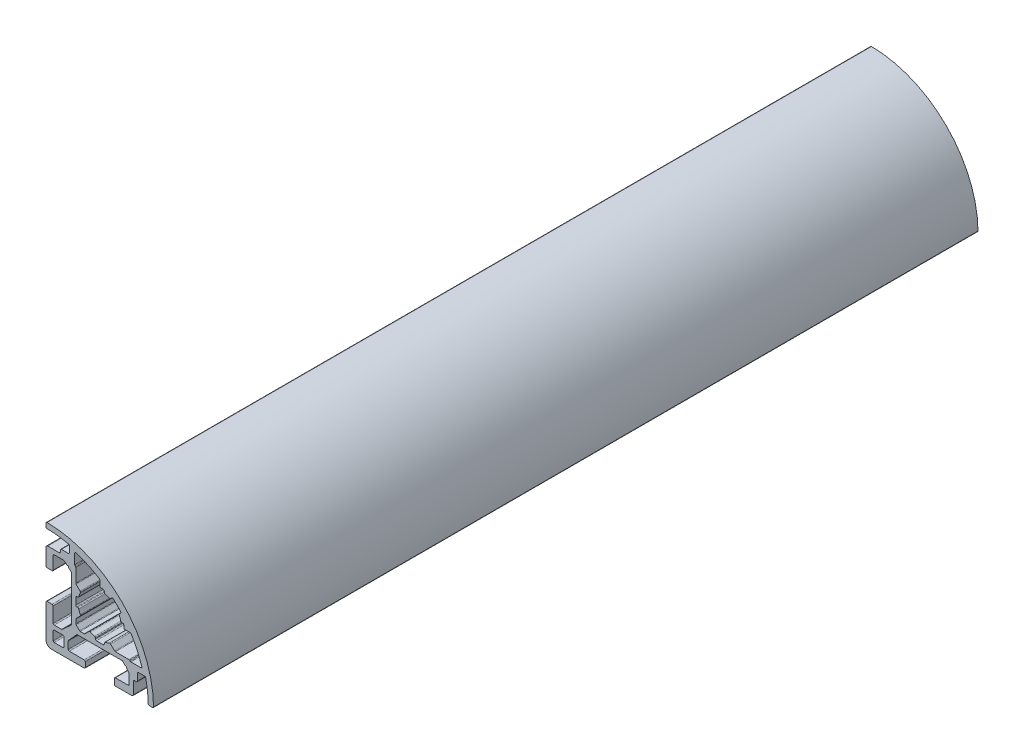
SolidWorks part; units mm, degrees
ref_plane "Plano frontal" through (0, 0, 0) normal (0, 0, 1) x (1, 0, 0)
ref_plane "Plano superior" through (0, 0, 0) normal (0, 1, 0) x (1, 0, 0)
ref_plane "Plano direito" through (0, 0, 0) normal (1, 0, 0) x (0, 0, -1)
ref_plane "Plano1" through (0, 0, 0) normal (0, 0, -1) x (-1, 0, 0)
sketch "Esboço1" plane through (0, 0, 0) normal (0, 0, -1) x (-1, 0, 0)
  line L0 (12.7, -13) -> (10.3, -13)
  line L1 (10, -12.7) -> (10, -10.3)
  line L2 (10.3, -10) -> (12.7, -10)
  line L3 (13, -10.3) -> (13, -12.7)
  line L4 (-0.95, 6.7) -> (-0.3, 6.7)
  line L5 (0, 7) -> (0, 8.4776)
  line L6 (7, 11.4273) -> (7, 8.6799)
  line L7 (6.9121, 8.4678) -> (6.7879, 8.3435)
  line L8 (6.7, 8.1314) -> (6.7, 4.3494)
  line L9 (6.6121, 4.1372) -> (5.4871, 3.0123)
  line L10 (6.1579, 1.25) -> (6.4, 1.25)
  line L11 (6.7, 0.95) -> (6.7, -0.95)
  line L12 (6.4, -1.25) -> (6.1579, -1.25)
  line L13 (5.4871, -3.0123) -> (6.6121, -4.1372)
  line L14 (6.7, -4.3494) -> (6.7, -5.4396)
  line L15 (6.6121, -5.6517) -> (5.6517, -6.6121)
  line L16 (5.4395, -6.7) -> (4.3494, -6.7)
  line L17 (4.1373, -6.6121) -> (3.0123, -5.4871)
  line L18 (1.25, -6.1579) -> (1.25, -6.4)
  line L19 (0.95, -6.7) -> (-0.95, -6.7)
  line L20 (-1.25, -6.4) -> (-1.25, -6.1579)
  line L21 (-3.0123, -5.4871) -> (-4.1373, -6.6121)
  line L22 (-4.3494, -6.7) -> (-8.1314, -6.7)
  line L23 (-8.3435, -6.7879) -> (-8.4678, -6.9121)
  line L24 (-8.6799, -7) -> (-11.4273, -7)
  line L25 (-8.4777, 0) -> (-7, 0)
  line L26 (-6.7, 0.3) -> (-6.7, 0.95)
  line L27 (-6.4, 1.25) -> (-6.1579, 1.25)
  line L28 (-5.4871, 3.0123) -> (-5.7974, 3.3226)
  line L29 (-3.3226, 5.7974) -> (-3.0123, 5.4871)
  line L30 (-1.25, 6.1579) -> (-1.25, 6.4)
  line L31 (7.9882, 6.432) -> (8.7045, 7.072)
  line L32 (8.7045, 7.072) -> (8.7283, 7.4958)
  line L33 (8.7283, 7.4958) -> (9.1516, 7.472)
  line L34 (9.1516, 7.472) -> (9.8678, 8.112)
  line L35 (10.08, 8.1999) -> (12.7001, 8.1998)
  line L36 (13.0001, 7.8998) -> (13, 4.3499)
  line L37 (13.3, 4.0499) -> (14.7, 4.0498)
  line L38 (15, 4.3498) -> (15, 8.8999)
  line L39 (14.5, 9.3999) -> (11.3, 9.3999)
  line L40 (11, 9.6999) -> (11, 10.1999)
  line L41 (10.7, 10.4999) -> (8.8, 10.4999)
  line L42 (8.5, 10.7999) -> (8.5, 12.51)
  line L43 (15, 13.7984) -> (15, 14.6985)
  line L44 (-14.6985, -15) -> (-13.7984, -15)
  line L45 (-12.5105, -8.5) -> (-10.8005, -8.5)
  line L46 (-10.5005, -8.8) -> (-10.5005, -10.7)
  line L47 (-10.2005, -11) -> (-9.7004, -11)
  line L48 (-9.4004, -11.3) -> (-9.4004, -14.5)
  line L49 (-8.9004, -15) -> (-4.3505, -15)
  line L50 (-4.0505, -14.7) -> (-4.0504, -13.3)
  line L51 (-4.3504, -13) -> (-7.9005, -12.9999)
  line L52 (-8.2005, -12.6999) -> (-8.2004, -10.0799)
  line L53 (-8.1126, -9.8677) -> (-7.4725, -9.1515)
  line L54 (-7.4725, -9.1515) -> (-7.4963, -8.728)
  line L55 (-7.4963, -8.728) -> (-7.0727, -8.7042)
  line L56 (-7.0727, -8.7042) -> (-6.4326, -7.988)
  line L57 (-6.2205, -7.9001) -> (6.2197, -7.9001)
  line L58 (6.4318, -7.988) -> (8.7117, -10.4679)
  line L59 (8.7996, -10.6801) -> (8.7996, -12.7001)
  line L60 (8.4996, -13.0001) -> (4.3496, -13.0001)
  line L61 (4.0496, -13.3001) -> (4.0496, -14.7)
  line L62 (4.3496, -15) -> (13.5, -15)
  line L63 (15, -13.5) -> (15, -4.3503)
  line L64 (14.7, -4.0503) -> (13.2999, -4.0503)
  line L65 (12.9999, -4.3503) -> (12.9999, -8.5003)
  line L66 (12.6999, -8.8003) -> (10.6798, -8.8003)
  line L67 (10.4677, -8.7124) -> (7.9878, -6.4325)
  line L68 (7.9003, -6.2203) -> (7.9003, 6.2198)
  arc A0 (10.3, -13) -> (10, -12.7) centre (10.3, -12.7) cw
  arc A1 (10, -10.3) -> (10.3, -10) centre (10.3, -10.3) cw
  arc A2 (12.7, -10) -> (13, -10.3) centre (12.7, -10.3) cw
  arc A3 (13, -12.7) -> (12.7, -13) centre (12.7, -12.7) cw
  arc A4 (-0.3, 6.7) -> (0, 7) centre (-0.3, 7) ccw
  arc A5 (0, 8.4776) -> (0.1408, 8.7319) centre (0.3, 8.4776) cw
  arc A6 (0.1408, 8.7319) -> (6.6101, 11.7135) centre (15, -15) cw
  arc A7 (6.6101, 11.7135) -> (7, 11.4273) centre (6.7, 11.4273) cw
  arc A8 (7, 8.6799) -> (6.9121, 8.4678) centre (6.7, 8.6799) cw
  arc A9 (6.7879, 8.3435) -> (6.7, 8.1314) centre (7, 8.1314) ccw
  arc A10 (6.7, 4.3494) -> (6.6121, 4.1372) centre (6.4, 4.3494) cw
  arc A11 (5.4871, 3.0123) -> (5.43, 2.6678) centre (5.6993, 2.8001) ccw
  arc A12 (5.43, 2.6678) -> (5.867, 1.4768) centre (0, 0) cw
  arc A13 (5.867, 1.4768) -> (6.1579, 1.25) centre (6.1579, 1.55) ccw
  arc A14 (6.4, 1.25) -> (6.7, 0.95) centre (6.4, 0.95) cw
  arc A15 (6.7, -0.95) -> (6.4, -1.25) centre (6.4, -0.95) cw
  arc A16 (6.1579, -1.25) -> (5.867, -1.4768) centre (6.1579, -1.55) ccw
  arc A17 (5.867, -1.4768) -> (5.43, -2.6678) centre (0, 0) cw
  arc A18 (5.43, -2.6678) -> (5.4871, -3.0123) centre (5.6993, -2.8001) ccw
  arc A19 (6.6121, -4.1372) -> (6.7, -4.3494) centre (6.4, -4.3494) cw
  arc A20 (6.7, -5.4396) -> (6.6121, -5.6517) centre (6.4, -5.4396) cw
  arc A21 (5.6517, -6.6121) -> (5.4395, -6.7) centre (5.4395, -6.4) cw
  arc A22 (4.3494, -6.7) -> (4.1373, -6.6121) centre (4.3494, -6.4) cw
  arc A23 (3.0123, -5.4871) -> (2.6678, -5.43) centre (2.8001, -5.6993) ccw
  arc A24 (2.6678, -5.43) -> (1.4768, -5.867) centre (0, 0) cw
  arc A25 (1.4768, -5.867) -> (1.25, -6.1579) centre (1.55, -6.1579) ccw
  arc A26 (1.25, -6.4) -> (0.95, -6.7) centre (0.95, -6.4) cw
  arc A27 (-0.95, -6.7) -> (-1.25, -6.4) centre (-0.95, -6.4) cw
  arc A28 (-1.25, -6.1579) -> (-1.4768, -5.867) centre (-1.55, -6.1579) ccw
  arc A29 (-1.4768, -5.867) -> (-2.6678, -5.43) centre (0, 0) cw
  arc A30 (-2.6678, -5.43) -> (-3.0123, -5.4871) centre (-2.8001, -5.6993) ccw
  arc A31 (-4.1373, -6.6121) -> (-4.3494, -6.7) centre (-4.3494, -6.4) cw
  arc A32 (-8.1314, -6.7) -> (-8.3435, -6.7879) centre (-8.1314, -7) ccw
  arc A33 (-8.4678, -6.9121) -> (-8.6799, -7) centre (-8.6799, -6.7) cw
  arc A34 (-11.4273, -7) -> (-11.7135, -6.6101) centre (-11.4273, -6.7) cw
  arc A35 (-11.7135, -6.6101) -> (-8.7319, -0.1408) centre (15, -15) cw
  arc A36 (-8.7319, -0.1408) -> (-8.4777, 0) centre (-8.4777, -0.3) cw
  arc A37 (-7, 0) -> (-6.7, 0.3) centre (-7, 0.3) ccw
  arc A38 (-6.7, 0.95) -> (-6.4, 1.25) centre (-6.4, 0.95) cw
  arc A39 (-6.1579, 1.25) -> (-5.867, 1.4768) centre (-6.1579, 1.55) ccw
  arc A40 (-5.867, 1.4768) -> (-5.43, 2.6678) centre (0, 0) cw
  arc A41 (-5.43, 2.6678) -> (-5.4871, 3.0123) centre (-5.6993, 2.8001) ccw
  arc A42 (-5.7974, 3.3226) -> (-5.8083, 3.7354) centre (-5.5853, 3.5347) cw
  arc A43 (-5.8083, 3.7354) -> (-3.7354, 5.8083) centre (15, -15) cw
  arc A44 (-3.7354, 5.8083) -> (-3.3226, 5.7974) centre (-3.5347, 5.5853) cw
  arc A45 (-3.0123, 5.4871) -> (-2.6678, 5.43) centre (-2.8001, 5.6993) ccw
  arc A46 (-2.6678, 5.43) -> (-1.4768, 5.867) centre (0, 0) cw
  arc A47 (-1.4768, 5.867) -> (-1.25, 6.1579) centre (-1.55, 6.1579) ccw
  arc A48 (-1.25, 6.4) -> (-0.95, 6.7) centre (-0.95, 6.4) cw
  arc A49 (9.8678, 8.112) -> (10.08, 8.1999) centre (10.08, 7.8999) cw
  arc A50 (12.7001, 8.1998) -> (13.0001, 7.8998) centre (12.7001, 7.8998) cw
  arc A51 (13, 4.3499) -> (13.3, 4.0499) centre (13.3, 4.3499) ccw
  arc A52 (14.7, 4.0498) -> (15, 4.3498) centre (14.7, 4.3498) ccw
  arc A53 (15, 8.8999) -> (14.5, 9.3999) centre (14.5, 8.8999) ccw
  arc A54 (11.3, 9.3999) -> (11, 9.6999) centre (11.3, 9.6999) cw
  arc A55 (11, 10.1999) -> (10.7, 10.4999) centre (10.7, 10.1999) ccw
  arc A56 (8.8, 10.4999) -> (8.5, 10.7999) centre (8.8, 10.7999) cw
  arc A57 (8.5, 12.51) -> (8.734, 12.8026) centre (8.8, 12.51) cw
  arc A58 (8.734, 12.8026) -> (14.7031, 13.4984) centre (15, -15) cw
  arc A59 (14.7031, 13.4984) -> (15, 13.7984) centre (14.7, 13.7984) ccw
  arc A60 (15, 14.6985) -> (14.697, 14.9985) centre (14.7, 14.6985) ccw
  arc A61 (14.697, 14.9985) -> (-14.9985, -14.697) centre (15, -15) ccw
  arc A62 (-14.9985, -14.697) -> (-14.6985, -15) centre (-14.6985, -14.7) ccw
  arc A63 (-13.7984, -15) -> (-13.4985, -14.7031) centre (-13.7984, -14.7) ccw
  arc A64 (-13.4985, -14.7031) -> (-12.8027, -8.734) centre (15, -15) cw
  arc A65 (-12.8027, -8.734) -> (-12.5105, -8.5) centre (-12.51, -8.8) cw
  arc A66 (-10.8005, -8.5) -> (-10.5005, -8.8) centre (-10.8005, -8.8) cw
  arc A67 (-10.5005, -10.7) -> (-10.2005, -11) centre (-10.2005, -10.7) ccw
  arc A68 (-9.7004, -11) -> (-9.4004, -11.3) centre (-9.7004, -11.3) cw
  arc A69 (-9.4004, -14.5) -> (-8.9004, -15) centre (-8.9004, -14.5) ccw
  arc A70 (-4.3505, -15) -> (-4.0505, -14.7) centre (-4.3505, -14.7) ccw
  arc A71 (-4.0504, -13.3) -> (-4.3504, -13) centre (-4.3504, -13.3) ccw
  arc A72 (-7.9005, -12.9999) -> (-8.2005, -12.6999) centre (-7.9005, -12.6999) cw
  arc A73 (-8.2004, -10.0799) -> (-8.1126, -9.8677) centre (-7.9004, -10.0799) cw
  arc A74 (-6.4326, -7.988) -> (-6.2205, -7.9001) centre (-6.2205, -8.2001) cw
  arc A75 (6.2197, -7.9001) -> (6.4318, -7.988) centre (6.2197, -8.2001) cw
  arc A76 (8.7117, -10.4679) -> (8.7996, -10.6801) centre (8.4996, -10.6801) cw
  arc A77 (8.7996, -12.7001) -> (8.4996, -13.0001) centre (8.4996, -12.7001) cw
  arc A78 (4.3496, -13.0001) -> (4.0496, -13.3001) centre (4.3496, -13.3001) ccw
  arc A79 (4.0496, -14.7) -> (4.3496, -15) centre (4.3496, -14.7) ccw
  arc A80 (13.5, -15) -> (15, -13.5) centre (13.5, -13.5) ccw
  arc A81 (15, -4.3503) -> (14.7, -4.0503) centre (14.7, -4.3503) ccw
  arc A82 (13.2999, -4.0503) -> (12.9999, -4.3503) centre (13.2999, -4.3503) ccw
  arc A83 (12.9999, -8.5003) -> (12.6999, -8.8003) centre (12.6999, -8.5003) cw
  arc A84 (10.6798, -8.8003) -> (10.4677, -8.7124) centre (10.6798, -8.5003) cw
  arc A85 (7.9878, -6.4325) -> (7.9003, -6.2203) centre (8.2003, -6.2208) cw
  arc A86 (7.9003, 6.2198) -> (7.9882, 6.432) centre (8.2003, 6.2198) cw
  dimension "D1" = 30
  dimension "D2" = 1.5
extrude "Ressalto-extrusão1" add sketch "Esboço1" against normal blind 230
sketch "Esboço2" plane through (0, 0, 0) normal (0, 0, -1) x (-1, 0, 0)
  line L0 (14.5607, -14.5607) -> (-6.2132, 6.2132) construction
  arc A0 (13.5, -15) -> (15, -13.5) centre (13.5, -13.5) ccw construction
  arc A1 (14.697, 14.9985) -> (-14.9985, -14.697) centre (15, -15) ccw construction
